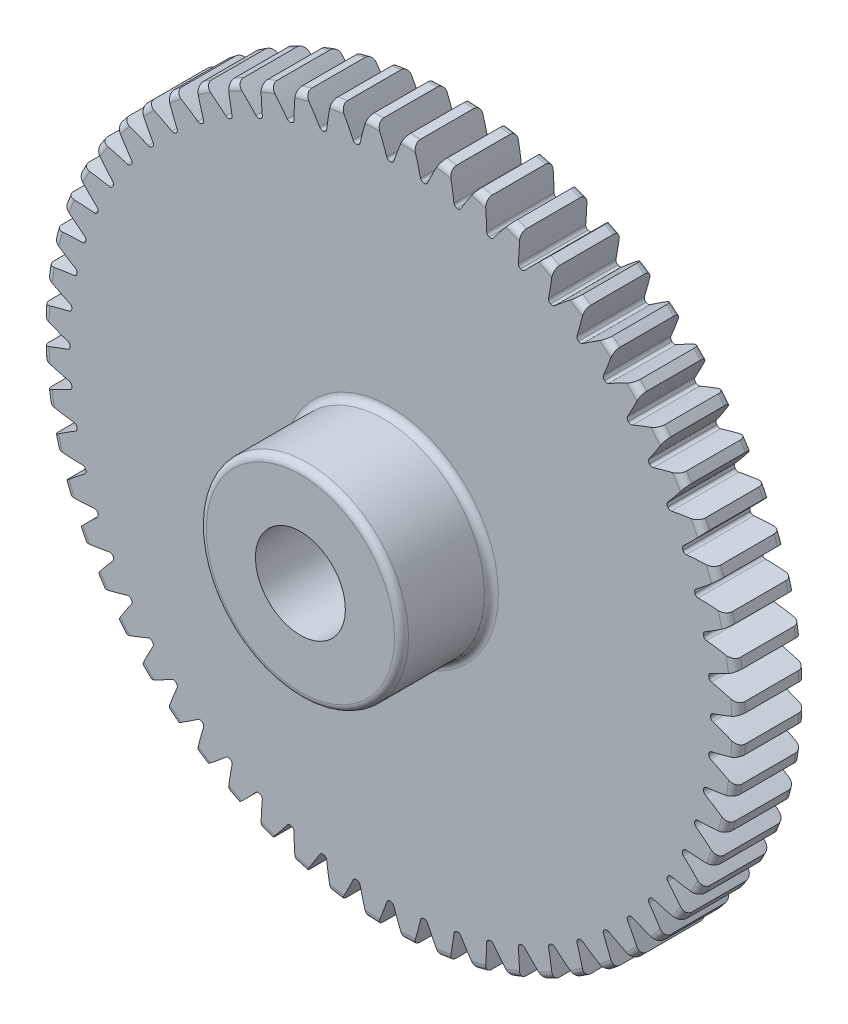
SolidWorks part; units mm, degrees
ref_plane "Front Plane" through (0, 0, 0) normal (0, 0, 1) x (1, 0, 0)
ref_plane "Top Plane" through (0, 0, 0) normal (0, 1, 0) x (1, 0, 0)
ref_plane "Right Plane" through (0, 0, 0) normal (1, 0, 0) x (0, 0, -1)
sketch "Sketch1" plane through (0, 0, 0) normal (0, 0, 1) x (1, 0, 0)
  line L0 (-762, 0) -> (762, 0) construction
  circle A0 centre (0, 0) radius 31 construction
  circle A1 centre (0, 0) radius 30 construction
  circle A2 centre (0, 0) radius 28.5 construction
  circle A3 centre (0, 0) radius 9 construction
  circle A4 centre (0, 0) radius 4 construction
  dimension "D2" = 1
  dimension "D3" = 2.5
  dimension "D1" = 2.5
sketch "Sketch2" plane through (0, 0, 0) normal (1, 0, 0) x (0, 0, -1)
  line L0 (0, 0) -> (-6, 0) construction
  line L1 (-6, 0) -> (-14, 0) construction
  dimension "Overall Width" = 14
  dimension "Face Width" = 6
sketch "Sketch4" plane through (0, 0, 0) normal (1, 0, 0) x (0, 0, -1)
  line L0 (-14, 4) -> (-14, 9)
  line L1 (-14, 9) -> (-6, 9)
  line L2 (-6, 9) -> (-6, 31)
  line L3 (-6, 31) -> (0, 31)
  line L4 (0, 31) -> (0, 4)
  line L5 (-6, 9) -> (-6, 0) construction
  line L6 (0, 31) -> (0, -31) construction
  line L7 (-6, 9) -> (0, 9) construction
  line L12 (-14, 4) -> (0, 4)
revolve "Revolve1" add sketch "Sketch4" angle 360 about L1
fillet "Fillet2" radius 0.62 4 edges at (0, 9, 14) (0, 9, 6) (0, 31, 6) (0, 31, 0)
sketch "Sketch7" plane through (0, 0, 6) normal (0, 0, 1) x (1, 0, 0)
  line L0 (0, 0) -> (0, 31) construction
  line L1 (0.7853, 29.9897) -> (1.1745, 30.9777) construction
  line L3 (1.6224, 30.9575) -> (1.5701, 29.9589) construction
  line L4 (1.5701, 29.9589) -> (1.4916, 28.4609) construction
  line L5 (0, 0) -> (1.4916, 28.4609) construction
  line L6 (0.7853, 29.9897) -> (0, 0) construction
  line L7 (0.7853, 29.9897) -> (0.8115, 30.9894) construction
  line L8 (0.7853, 29.9897) -> (0, 0) construction
  circle A0 centre (0, 0) radius 31 construction
  arc A1 (-0.0279, 28.5) -> (0.0279, 28.5) centre (0, 0) cw
  circle A2 centre (0, 0) radius 28.5 construction
  arc A3 (-0.7853, 29.9897) -> (0.7853, 29.9897) centre (0, 0) cw construction
  circle A4 centre (0, 0) radius 30 construction
  arc A5 (2.0499, 30.9322) -> (1.1947, 30.977) centre (0, 0) ccw construction
  arc A6 (0.7853, 29.9897) -> (2.3538, 29.9075) centre (0, 0) cw construction
  arc A7 (-1.1947, 30.977) -> (1.1947, 30.977) centre (0, 0) cw
  arc A8 (0.3121, 28.7029) -> (1.1947, 30.977) centre (28.6978, 18.9947) cw
  arc A9 (-0.3121, 28.7029) -> (-1.1947, 30.977) centre (-28.6978, 18.9947) ccw
  arc A10 (-0.0279, 28.5) -> (-0.3121, 28.7029) centre (-0.0282, 28.8) cw
  arc A11 (0.0279, 28.5) -> (0.3121, 28.7029) centre (0.0282, 28.8) ccw
  point P26 (-0.2432, 28.499)
  point P29 (0.2432, 28.499)
  dimension "D4" = 0.3
  dimension "D5" = 30
  dimension "D3" = 20
  dimension "D1" = 3.1416
  dimension "D2" = 1.5708
extrude "Cut-Extrude2" cut sketch "Sketch7" against normal through all
pattern_circular "CirPattern1" count 60 over 360 about axis through (0, 0, 0) along (0, 0, 1) of "Cut-Extrude2"
equation "\"D1@Sketch1\"=2.5*(\"Pitch Dia.@Sketch1\"/\"Number of Teeth@Sketch1\")"
equation "\"D1@CirPattern1\"=\"Number of Teeth@Sketch1\""
equation "\"D1@Fillet2\"=\"OD@Sketch1\"*.01"
equation "\"D1@Sketch7\"=3.14159*(\"Pitch Dia.@Sketch1\"/\"Number of Teeth@Sketch1\")"
equation "\"D2@Sketch7\"=\"D1@Sketch7\"/2"
equation "\"D4@Sketch7\"=\"D1@Sketch7\"*.0955"
equation "\"D5@Sketch7\"=\"Pitch Dia.@Sketch1\"/2"
